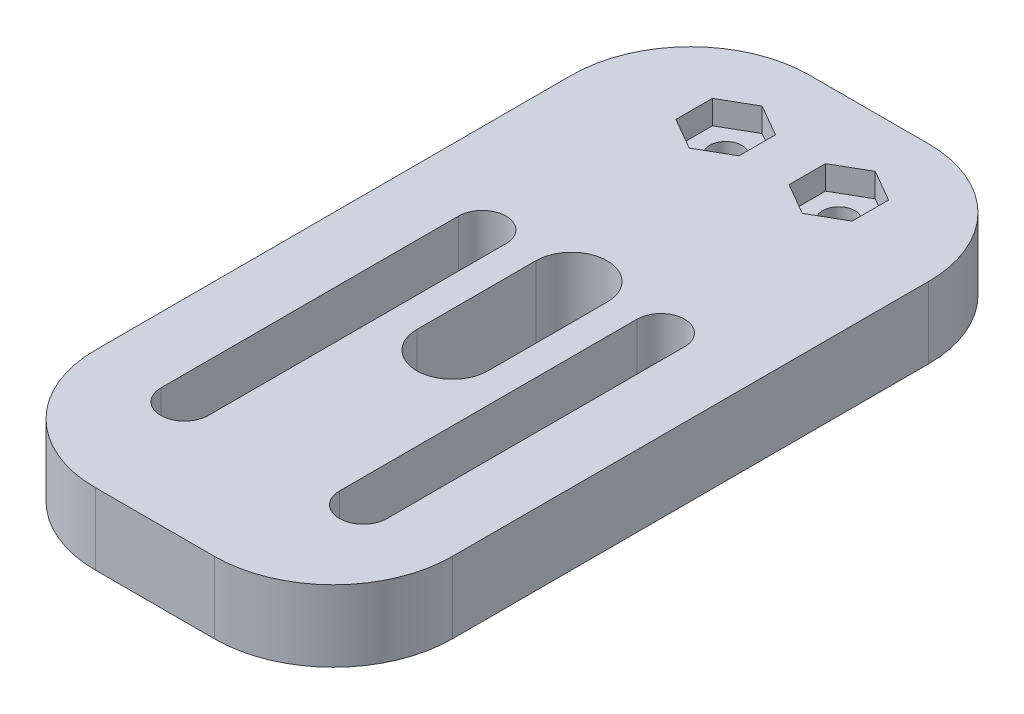
SolidWorks part; units mm, degrees
ref_plane "Alzado" through (0, 0, 0) normal (0, 0, 1) x (1, 0, 0)
ref_plane "Planta" through (0, 0, 0) normal (0, 1, 0) x (1, 0, 0)
ref_plane "Vista lateral" through (0, 0, 0) normal (1, 0, 0) x (0, 0, -1)
sketch "Croquis2" plane through (0, 0, 0) normal (0, 1, 0) x (1, 0, 0)
  line L0 (0, 0) -> (0, 57.2245) construction
  line L1 (-15, 0) -> (15, 0)
  line L2 (-15, 0) -> (-15, 60)
  line L3 (-15, 60) -> (15, 60)
  line L4 (15, 0) -> (15, 60)
  line L5 (-7.5, 35) -> (-7.5, 10) construction
  line L6 (-5.5, 35) -> (-5.5, 10)
  line L7 (-9.5, 35) -> (-9.5, 10)
  line L8 (7.5, 35) -> (7.5, 10) construction
  line L9 (9.5, 35) -> (9.5, 10)
  line L10 (5.5, 35) -> (5.5, 10)
  line L11 (0, 35) -> (0, 25) construction
  line L12 (3, 35) -> (3, 25)
  line L13 (-3, 35) -> (-3, 25)
  arc A0 (-5.5, 35) -> (-9.5, 35) centre (-7.5, 35) ccw
  arc A1 (-9.5, 10) -> (-5.5, 10) centre (-7.5, 10) ccw
  arc A2 (9.5, 35) -> (5.5, 35) centre (7.5, 35) ccw
  arc A3 (5.5, 10) -> (9.5, 10) centre (7.5, 10) ccw
  arc A4 (3, 35) -> (-3, 35) centre (0, 35) ccw
  arc A5 (-3, 25) -> (3, 25) centre (0, 25) ccw
  point P8 (-7.5, 22.5)
  point P14 (7.5, 22.5)
  point P23 (0, 30)
  dimension "D3" = 2
  dimension "D9" = 3
  dimension "D1" = 60
  dimension "D2" = 30
  dimension "D4" = 10
  dimension "D5" = 25
  dimension "D6" = 15
  dimension "D7" = 25
  dimension "D8" = 10
extrude "Saliente-Extruir1" add sketch "Croquis2" along normal blind 6
fillet "Redondeo1" radius 10 2 edges at (-15, 3, -60) (15, 3, -60)
fillet "Redondeo2" radius 10 2 edges at (-15, 3, 0) (15, 3, 0)
sketch "Croquis3" plane through (0, 0, 0) normal (0, -1, 0) x (1, 0, 0)
  line L0 (5, -60) -> (-5, -60) construction
  line L1 (-15, -50) -> (-15, -10) construction
  circle A0 centre (4.75, -52.7) radius 1.35
  circle A1 centre (-4.75, -52.7) radius 1.35
  dimension "D4" = 2.7
  dimension "D1" = 7.3
  dimension "D2" = 10.25
  dimension "D3" = 9.5
extrude "Cortar-Extruir1" cut sketch "Croquis3" against normal through all
sketch "Croquis4" plane through (0, 6, 0) normal (0, -1, 0) x (-1, 0, 0)
  line L1 (-2.1, 51.17) -> (-2.1, 54.23)
  line L2 (-2.1, 54.23) -> (-4.75, 55.76)
  line L3 (-4.75, 55.76) -> (-7.4, 54.23)
  line L4 (-7.4, 54.23) -> (-7.4, 51.17)
  line L5 (-7.4, 51.17) -> (-4.75, 49.64)
  line L6 (-4.75, 49.64) -> (-2.1, 51.17)
  line L7 (7.4, 51.17) -> (7.4, 54.23)
  line L8 (7.4, 54.23) -> (4.75, 55.76)
  line L9 (4.75, 55.76) -> (2.1, 54.23)
  line L10 (2.1, 54.23) -> (2.1, 51.17)
  line L11 (2.1, 51.17) -> (4.75, 49.64)
  line L12 (4.75, 49.64) -> (7.4, 51.17)
  circle A0 centre (-4.75, 52.7) radius 2.65 construction
  circle A1 centre (4.75, 52.7) radius 2.65 construction
  dimension "D1" = 5.3
extrude "Cortar-Extruir2" cut sketch "Croquis4" along normal blind 2
